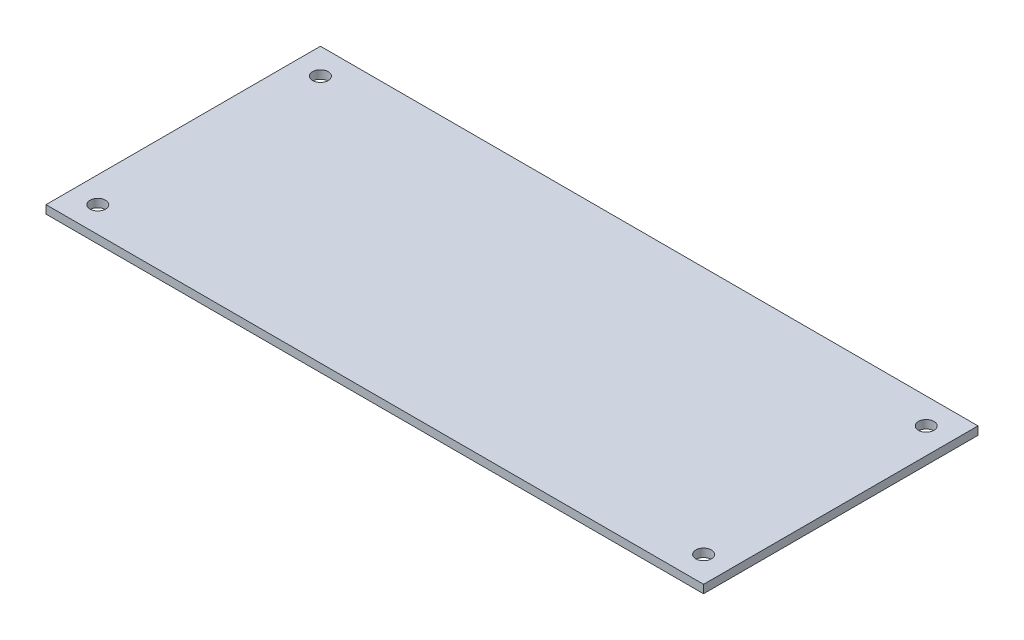
SolidWorks part; units mm, degrees
ref_plane "Front Plane" through (0, 0, 0) normal (0, 0, 1) x (1, 0, 0)
ref_plane "Top Plane" through (0, 0, 0) normal (0, 1, 0) x (1, 0, 0)
ref_plane "Right Plane" through (0, 0, 0) normal (1, 0, 0) x (0, 0, -1)
sketch "Sketch1" plane through (0, 0, 0) normal (0, 1, 0) x (1, 0, 0)
  line L0 (-63.5, -26.5) -> (63.5, -26.5)
  line L1 (-63.5, -26.5) -> (-63.5, 26.5)
  line L2 (63.5, -26.5) -> (63.5, 26.5)
  line L3 (-63.5, 26.5) -> (63.5, 26.5)
  line L4 (-63.5, -26.5) -> (63.5, 26.5) construction
  line L5 (63.5, -26.5) -> (-63.5, 26.5) construction
  point P1 (0, 0)
  dimension "D1" = 127
  dimension "D2" = 53
extrude "Boss-Extrude1" add sketch "Sketch1" along normal blind 1.5875 contours L0 L2 L3 L1
sketch "Sketch2" plane through (0, 1.5875, 0) normal (0, 1, 0) x (1, 0, 0)
  line L8 (-58.5, 21.5) -> (-58.5, -21.5)
  line L9 (-58.5, -21.5) -> (58.5, -21.5)
  line L10 (58.5, -21.5) -> (58.5, 21.5)
  line L11 (58.5, 21.5) -> (-58.5, 21.5)
  line L12 (-58.5, 21.5) -> (-58.5, -21.5) construction
  line L13 (-58.5, -21.5) -> (58.5, -21.5) construction
  line L14 (58.5, -21.5) -> (58.5, 21.5) construction
  line L15 (58.5, 21.5) -> (-58.5, 21.5) construction
  circle A0 centre (-58.5, -21.5) radius 1.5
  circle A1 centre (58.5, -21.5) radius 1.5
  circle A2 centre (58.5, 21.5) radius 1.5
  circle A3 centre (-58.5, 21.5) radius 1.5
  dimension "D2" = 3
  dimension "D1" = 5
extrude "Cut-Extrude1" cut sketch "Sketch2" against normal through all
